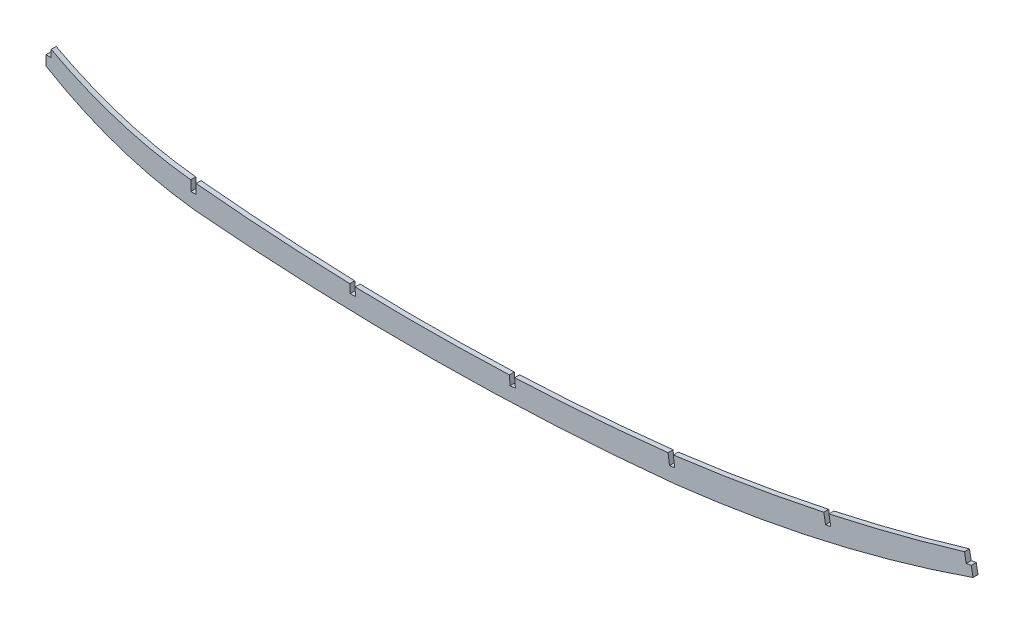
SolidWorks part; units mm, degrees
material "Plywood"
ref_plane "Front Plane" through (0, 0, 0) normal (0, 0, 1) x (1, 0, 0)
ref_plane "Top Plane" through (0, 0, 0) normal (0, 1, 0) x (1, 0, 0)
ref_plane "Right Plane" through (0, 0, 0) normal (1, 0, 0) x (0, 0, -1)
sketch "Sketch2" plane through (0, 0, 0) normal (0, 0, 1) x (1, 0, 0)
  line L0 (0, -94.4694) -> (0, -81.7694)
  line L1 (0, -94.4694) -> (93.98, -94.4694) construction
  line L2 (93.98, -126.4975) -> (93.98, -111.2575) construction
  line L3 (349.6407, -137.6462) -> (348.9613, -137.618) construction
  line L4 (349.6407, -137.6462) -> (354.8905, -137.8645) construction
  line L5 (93.98, -94.4694) -> (93.98, -126.4975) construction
  line L6 (400.2036, -124.7658) -> (400.2036, -94.4694) construction
  line L7 (590.8643, -81.3536) -> (588.5933, -68.8583)
  line L8 (0, 0) -> (672.417, 0) construction
  line L10 (93.98, -94.4694) -> (590.8643, -94.4694) construction
  line L11 (590.8643, -94.4694) -> (590.8643, -81.3536) construction
  line L12 (400.2036, -124.7658) -> (396.2207, -94.4694) construction
  arc A0 (0, -94.4694) -> (93.98, -126.4975) centre (121.7349, 108.8411) ccw
  arc A3 (93.98, -126.4975) -> (400.2036, -124.7658) centre (237.9716, 1487.1243) ccw
  arc A6 (400.2036, -124.7658) -> (590.8643, -81.3536) centre (300.4984, 753.5129) ccw
  arc A7 (93.98, -111.2575) -> (398.1841, -109.4039) centre (237.3586, 1321.3743) ccw
  arc A10 (0, -81.7694) -> (93.98, -111.2575) centre (118.1544, 130.2915) ccw
  arc A11 (398.1841, -109.4039) -> (588.5933, -68.8583) centre (254.6725, 1031.9221) ccw
  dimension "D3" = 236.9696
  dimension "D4" = 30.2963
  dimension "D5" = 400.2036
  dimension "D6" = 79.699
  dimension "D7" = 82.511
  dimension "D8" = 15.24
  dimension "D11" = 242.7557
  dimension "D14" = 1620.0336
  dimension "D15" = 883.92
  dimension "D16" = 15.494
  dimension "D18" = 1150.3133
  dimension "D1" = 12.7
  dimension "D2" = 81.7694
  dimension "D9" = 32.028
  dimension "D10" = 93.98
  dimension "D12" = 13.1158
  dimension "D13" = 496.8843
  dimension "D17" = 12.7
extrude "Boss-Extrude1" add sketch "Sketch2" along normal blind 3.175
sketch "Sketch3" plane through (0, 0, 3.175) normal (0, 0, 1) x (1, 0, 0)
  line L0 (0, 0) -> (0, -81.8237) construction
  line L1 (0, 0) -> (93.98, 0) construction
  line L2 (93.98, 0) -> (93.98, -117.6075) construction
  line L4 (0, -81.8237) -> (0, -88.1813)
  line L5 (0, -88.1813) -> (3.302, -88.1813)
  line L6 (3.302, -81.8237) -> (3.302, -88.1813)
  line L7 (193.9543, -123.223) -> (197.1266, -123.0902)
  line L8 (0, -81.8237) -> (0, -80.8493)
  line L9 (0, -80.8493) -> (3.302, -80.8493)
  line L10 (3.302, -80.8493) -> (3.302, -81.8237)
  line L11 (186.3309, 134.7479) -> (183.1587, 134.6151)
  line L12 (92.2909, -117.5313) -> (95.6691, -117.5313)
  line L13 (92.2909, -117.5313) -> (92.2909, -108.4147)
  line L14 (92.2909, -108.4147) -> (95.6691, -108.4147)
  line L15 (95.6691, -117.5313) -> (95.6691, -108.4147)
  line L16 (193.687, -116.8375) -> (196.8592, -116.7047)
  line L17 (186.5983, 128.3624) -> (183.4261, 128.2296)
  line L18 (197.1266, -123.0902) -> (196.8592, -116.7047)
  line L19 (186.5983, 128.3624) -> (186.3309, 134.7479)
  line L20 (193.9543, -123.223) -> (193.687, -116.8375)
  line L21 (183.4261, 128.2296) -> (183.1587, 134.6151)
  line L22 (183.4261, 128.2296) -> (183.1587, 134.6151)
  line L24 (186.5983, 128.3624) -> (186.3309, 134.7479)
  line L26 (186.5983, 128.3624) -> (183.4261, 128.2296)
  line L28 (186.3309, 134.7479) -> (183.1587, 134.6151)
  line L30 (195.5404, -123.1566) -> (190.3839, 0) construction
  line L31 (93.98, 0) -> (612.4013, 0) construction
  line L32 (574.4157, 0) -> (588.1634, -75.3909) construction
  line L33 (193.8496, -123.1511) -> (197.2249, -123.0098)
  line L34 (193.8496, -123.1511) -> (193.5511, -116.0212)
  line L35 (197.2249, -123.0098) -> (196.9263, -115.8799)
  line L36 (193.5511, -116.0212) -> (196.9263, -115.8799)
  line L37 (397.3751, -116.2998) -> (400.7239, -115.855)
  line L38 (397.3751, -116.2998) -> (395.8625, -104.9127)
  line L39 (286.9301, 0) -> (297.4996, -122.788) construction
  line L40 (295.8233, -123.0088) -> (299.189, -122.7191)
  line L41 (295.8233, -123.0088) -> (295.1616, -115.3225)
  line L42 (299.189, -122.7191) -> (298.5274, -115.0328)
  line L43 (295.1616, -115.3225) -> (298.5274, -115.0328)
  line L44 (383.6307, 0) -> (399.0395, -116.0018) construction
  line L45 (400.7239, -115.855) -> (399.2113, -104.4679)
  line L46 (395.8625, -104.9127) -> (399.2113, -104.4679)
  line L48 (586.5153, -75.7689) -> (589.8387, -75.1629)
  line L49 (480.4996, 0) -> (498.5238, -98.843) construction
  line L50 (496.8758, -99.221) -> (500.1992, -98.615)
  line L51 (496.8758, -99.221) -> (495.4086, -91.1748)
  line L52 (500.1992, -98.615) -> (498.732, -90.5688)
  line L53 (495.4086, -91.1748) -> (498.732, -90.5688)
  line L56 (586.5153, -75.7689) -> (585.2098, -68.6095)
  line L57 (589.8387, -75.1629) -> (588.5332, -68.0035)
  line L58 (585.2098, -68.6095) -> (588.5332, -68.0035)
  point P14 (93.98, -108.4147)
  point P25 (195.2387, -115.9505)
  point P28 (297.5062, -122.864)
  point P31 (399.0495, -116.0774)
  point P39 (498.5375, -98.918)
  point P51 (588.177, -75.4659)
  dimension "D1" = 81.8237
  dimension "D2" = 6.3576
  dimension "D3" = 3.302
  dimension "D4" = 93.98
  dimension "D5" = 117.6075
  dimension "D6" = 3.3782
  dimension "D7" = 0.0762
  dimension "D8" = 92.398
  dimension "D9" = 0.0762
  dimension "D10" = 3.3782
  dimension "D11" = 190.3839
  dimension "D12" = 123.2645
  dimension "D13" = 94.92
  dimension "D14" = 96.5461
  dimension "D15" = 123.2421
  dimension "D16" = 0.0762
  dimension "D17" = 3.3782
  dimension "D18" = 96.7007
  dimension "D19" = 97.566
  dimension "D20" = 117.0207
  dimension "D21" = 0.0762
  dimension "D22" = 3.3782
  dimension "D23" = 96.8689
  dimension "D24" = 100.334
  dimension "D25" = 100.473
  dimension "D26" = 3.3782
  dimension "D27" = 0.0762
  dimension "D28" = 93.9161
  dimension "D29" = 76.6341
  dimension "D30" = 100.334
  dimension "D31" = 0.0762
  dimension "D32" = 3.3782
extrude "Cut-Extrude2" cut sketch "Sketch3" against normal through all
